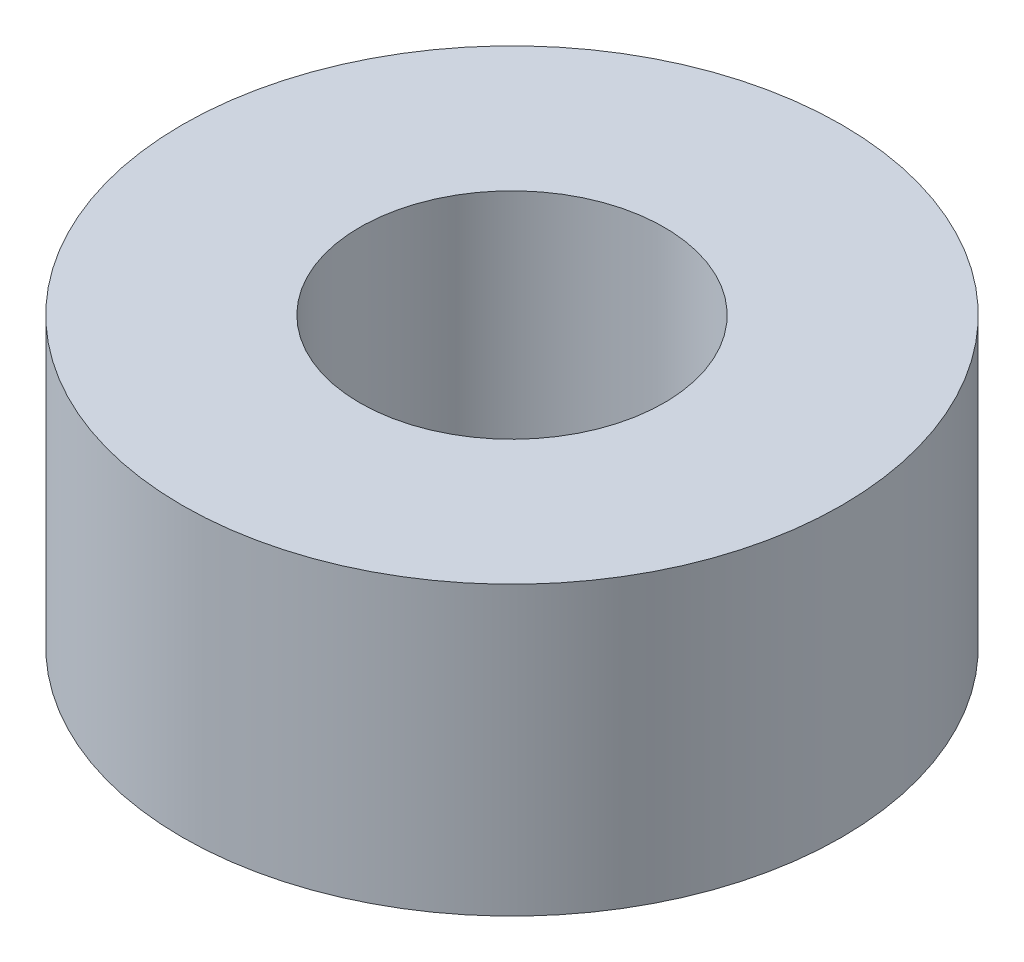
SolidWorks part; units mm, degrees
ref_plane "Front Plane" through (0, 0, 0) normal (0, 0, 1) x (1, 0, 0)
ref_plane "Top Plane" through (0, 0, 0) normal (0, 1, 0) x (1, 0, 0)
ref_plane "Right Plane" through (0, 0, 0) normal (1, 0, 0) x (0, 0, -1)
sketch "Sketch1" plane through (0, 0, 0) normal (0, 1, 0) x (1, 0, 0)
  circle A0 centre (0, 0) radius 1.95
  circle A1 centre (0, 0) radius 0.9
  dimension "D1" = 3.9
  dimension "D2" = 1.8
extrude "Boss-Extrude1" add sketch "Sketch1" along normal blind 1.7
